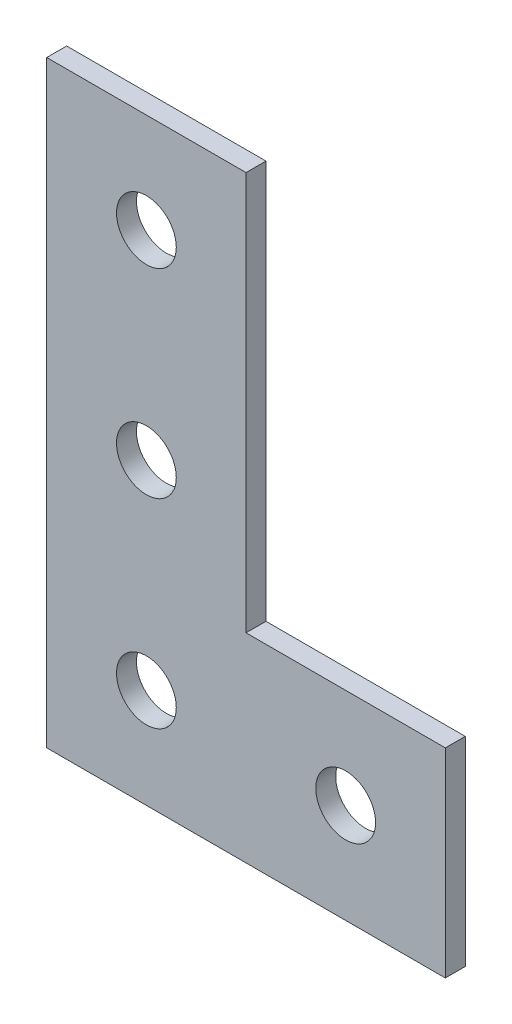
SolidWorks part; units mm, degrees
ref_plane "Front Plane" through (0, 0, 0) normal (0, 0, 1) x (1, 0, 0)
ref_plane "Top Plane" through (0, 0, 0) normal (0, 1, 0) x (1, 0, 0)
ref_plane "Right Plane" through (0, 0, 0) normal (1, 0, 0) x (0, 0, -1)
sketch "Esquisse1" plane through (0, 0, 0) normal (0, 0, 1) x (1, 0, 0)
  line L0 (0, 0) -> (20, 0)
  line L1 (20, 0) -> (20, 10)
  line L2 (20, 10) -> (10, 10)
  line L3 (10, 10) -> (10, 30)
  line L4 (10, 30) -> (0, 30)
  line L5 (0, 30) -> (0, 0)
  point P7 (19.9506, 1.4043)
  point P8 (9.3566, 30)
  dimension "D1" = 30
  dimension "D2" = 10
  dimension "D3" = 20
extrude "Boss.-Extru.1" add sketch "Esquisse1" along normal blind 1
sketch "Esquisse2" plane through (0, 0, 1) normal (0, 0, 1) x (1, 0, 0)
  line L0 (20, 0) -> (20, 10) construction
  line L1 (10, 30) -> (0, 30) construction
  circle A0 centre (5, 5) radius 1.5
  circle A1 centre (5, 15) radius 1.5
  circle A2 centre (5, 25) radius 1.5
  circle A3 centre (15, 5) radius 1.5
  point P6 (20, 5)
  point P10 (5, 30)
  dimension "D1" = 3
  dimension "D4" = 10
  dimension "D2" = 10
  dimension "D3" = 10
extrude "Enlèv. mat.-Extru.1" cut sketch "Esquisse2" against normal through all
